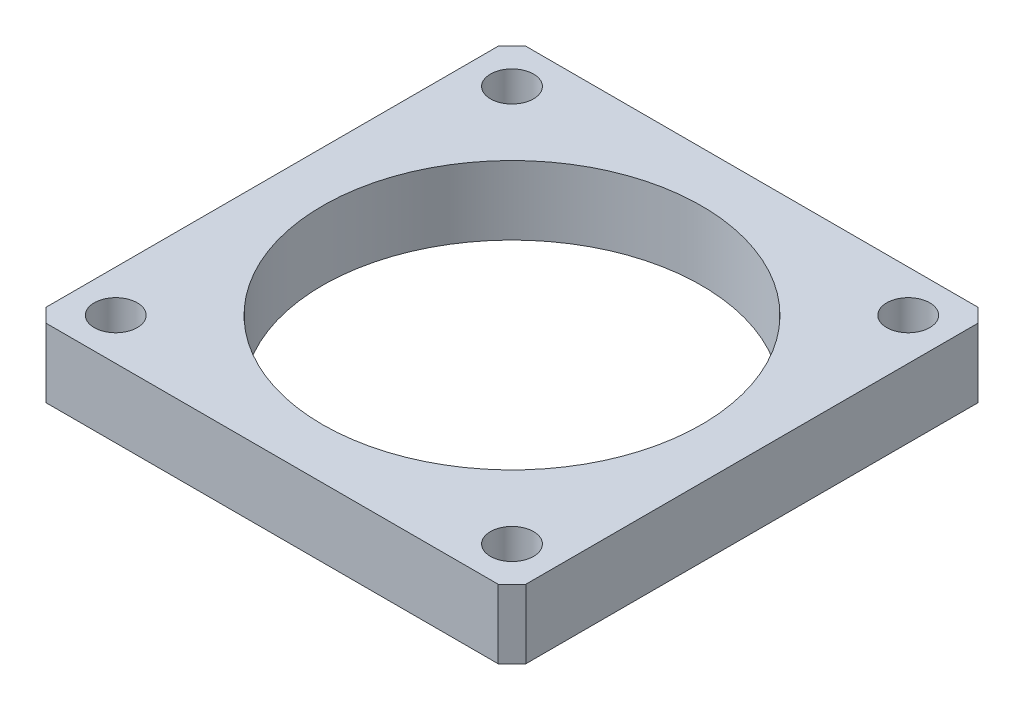
SolidWorks part; units mm, degrees
ref_plane "Спереди" through (0, 0, 0) normal (0, 0, 1) x (1, 0, 0)
ref_plane "Сверху" through (0, 0, 0) normal (0, 1, 0) x (1, 0, 0)
ref_plane "Справа" through (0, 0, 0) normal (1, 0, 0) x (0, 0, -1)
sketch "Эскиз2" plane through (0, 0, 0) normal (0, 1, 0) x (1, 0, 0)
  line L1 (-13.925, -13.925) -> (13.925, -13.925)
  line L2 (-13.925, -13.925) -> (-13.925, 13.925)
  line L3 (-13.925, 13.925) -> (13.925, 13.925)
  line L4 (13.925, -13.925) -> (13.925, 13.925)
  line L5 (-15.1489, -15.1489) -> (15.1496, 15.1496) construction
  line L6 (-15.2392, 15.2392) -> (15.2392, -15.2392) construction
  line L7 (11.5, -11.5) -> (-11.5, -11.5) construction
  line L8 (11.5, -11.5) -> (11.5, 11.5) construction
  line L9 (11.5, 11.5) -> (-11.5, 11.5) construction
  line L10 (-11.5, -11.5) -> (-11.5, 11.5) construction
  line L11 (11.5, -11.5) -> (-11.5, 11.5) construction
  line L12 (11.5, 11.5) -> (-11.5, -11.5) construction
  circle A4 centre (-11.5, 11.5) radius 1.25
  circle A5 centre (-11.5, -11.5) radius 1.25
  circle A6 centre (11.5, -11.5) radius 1.25
  circle A7 centre (11.5, 11.5) radius 1.25
  circle A8 centre (0, 0) radius 11
  point P0 (0, 0)
  point P24 (0, 13.925)
  dimension "D1" = 2.5
  dimension "D2" = 23
  dimension "D4" = 22
  dimension "D3" = 27.85
extrude "Бобышка-Вытянуть1" add sketch "Эскиз2" along normal blind 4
chamfer "Фаска1" distance 0.8 angle 45 4 edges at (13.925, 2, -13.925) (13.925, 2, 13.925) (-13.925, 2, 13.925) (-13.925, 2, -13.925)
